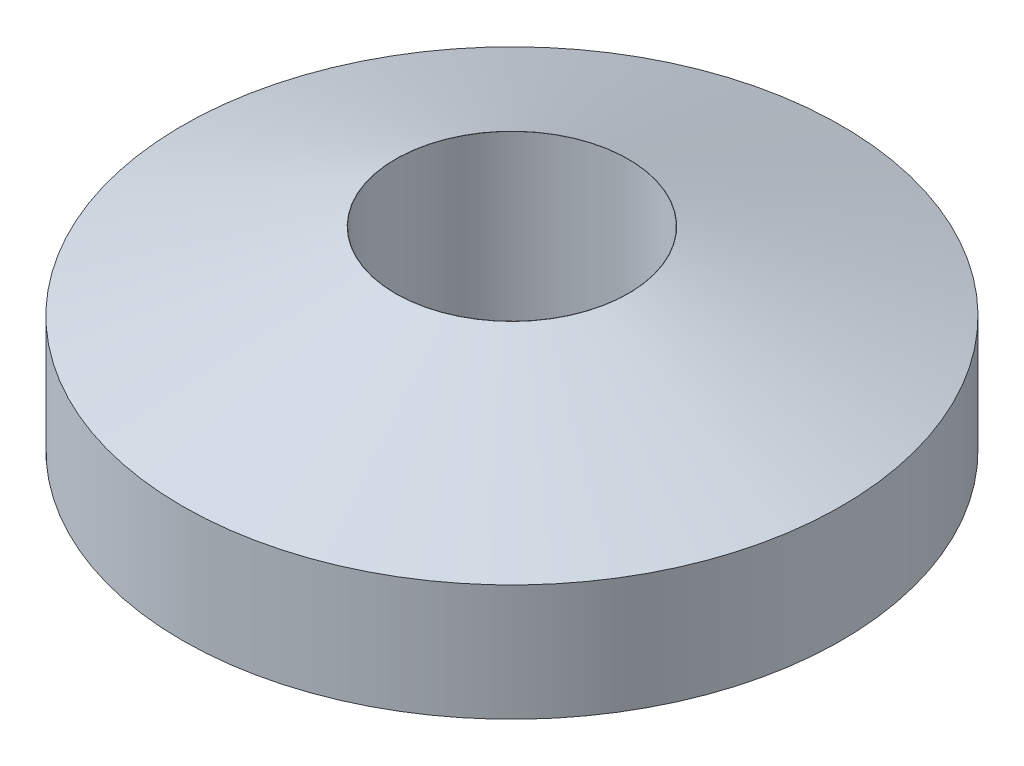
SolidWorks part; units mm, degrees
material "Caucho"
ref_plane "Alzado" through (0, 0, 0) normal (0, 0, 1) x (1, 0, 0)
ref_plane "Planta" through (0, 0, 0) normal (0, 1, 0) x (1, 0, 0)
ref_plane "Vista lateral" through (0, 0, 0) normal (1, 0, 0) x (0, 0, -1)
sketch "Croquis1" plane through (0, 0, 0) normal (0, 1, 0) x (1, 0, 0)
  circle A0 centre (0, 0) radius 8.5
  dimension "D1" = 17
extrude "Saliente-Extruir1" add sketch "Croquis1" along normal blind 5
sketch "Croquis2" plane through (0, 5, 0) normal (0, 1, 0) x (1, 0, 0)
  circle A0 centre (0, 0) radius 3
  dimension "D1" = 6
extrude "Cortar-Extruir1" cut sketch "Croquis2" against normal blind 15
chamfer "Chaflán1" distance 2 angle 70 1 edges at (0, 5, 8.5)
